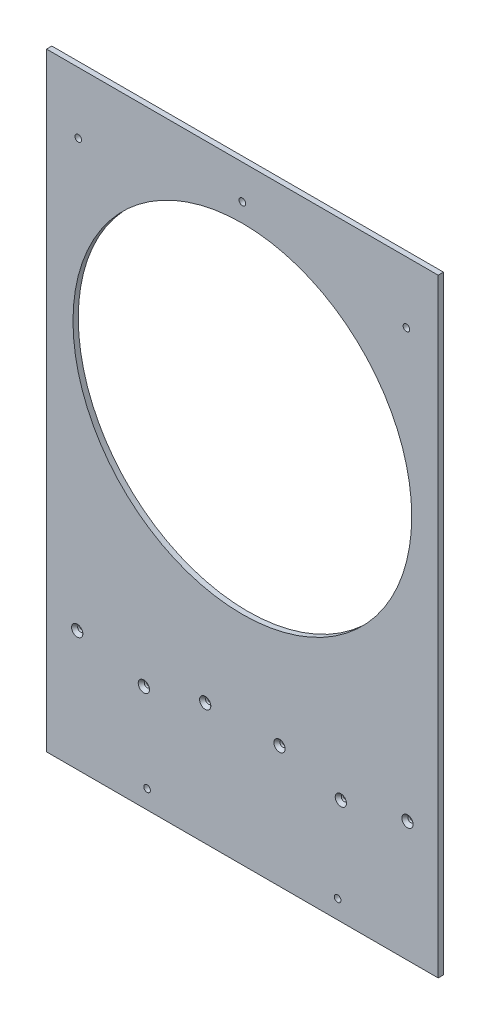
SolidWorks part; units mm, degrees
material "PC High Viscosity"
ref_plane "Front Plane" through (0, 0, 0) normal (0, 0, 1) x (1, 0, 0)
ref_plane "Top Plane" through (0, 0, 0) normal (0, 1, 0) x (1, 0, 0)
ref_plane "Right Plane" through (0, 0, 0) normal (1, 0, 0) x (0, 0, -1)
sketch "Sketch1" plane through (0, 0, 0) normal (0, 0, 1) x (1, 0, 0)
  line L0 (0, 695.96) -> (0, 1407.16) construction
  line L1 (-234.95, 0) -> (234.95, 0)
  line L2 (-234.95, 0) -> (-234.95, 2413)
  line L3 (-234.95, 2413) -> (234.95, 2413)
  line L4 (234.95, 0) -> (234.95, 2413)
  circle A0 centre (0, 695.96) radius 203.2
  circle A1 centre (0, 1407.16) radius 203.2
  circle A2 centre (0, 2118.36) radius 203.2
  dimension "D3" = 406.4
  dimension "D1" = 2413
  dimension "D2" = 469.9
  dimension "D4" = 492.76
  dimension "D6" = 711.2
  dimension "D5" = 3
extrude "Boss-Extrude1" add sketch "Sketch1" along normal blind 6.35
hole_wizard "CSK for 1/4 Flat Head Socket Cap Screw1" positions "Sketch2" profile "Sketch3" countersink size "1/4" standard "ANSI Inch"
sketch "Sketch2" plane through (0, 0, 6.35) normal (0, 0, 1) x (1, 0, 0)
  line L0 (0, 0) -> (0, 2413) construction
  line L1 (234.95, 2413) -> (-234.95, 2413) construction
  line L3 (2.839, 370.0053) -> (12.7, 406.807) construction
  line L4 (2.839, 370.0053) -> (225.089, 310.4536) construction
  line L5 (12.7, 406.807) -> (234.95, 347.2553) construction
  line L6 (225.089, 310.4536) -> (234.95, 347.2553) construction
  line L7 (234.95, 0) -> (234.95, 2413) construction
  line L8 (-234.95, 0) -> (234.95, 0) construction
  line L9 (7.7695, 388.4062) -> (230.0195, 328.8545) construction
  line L11 (118.1748, 358.8231) -> (118.1748, 1070.0231) construction
  line L12 (12.7, 406.807) -> (0, 410.21) construction
  line L14 (12.7, 406.807) -> (14.3435, 412.9407) construction
  line L15 (12.7, 406.807) -> (233.3065, 347.6957) construction
  line L16 (14.3435, 412.9407) -> (234.95, 353.8293) construction
  line L17 (233.3065, 347.6957) -> (234.95, 353.8293) construction
  circle A0 centre (198.12, 376.8459) radius 6.35 construction
  point P0 (44.5713, 378.5452)
  point P2 (118.1748, 358.8231)
  point P4 (-44.5713, 378.5452)
  point P6 (-118.1748, 358.8231)
  point P187 (44.5713, 1089.7452)
  point P188 (118.1748, 1070.0231)
  point P189 (-44.5713, 1089.7452)
  point P190 (-118.1748, 1070.0231)
  point P191 (44.5713, 1800.9452)
  point P192 (118.1748, 1781.2231)
  point P193 (-44.5713, 1800.9452)
  point P194 (-118.1748, 1781.2231)
  point P380 (198.12, 376.8459)
  point P382 (-198.12, 376.8459)
  point P386 (-198.12, 1088.0459)
  point P387 (-198.12, 1799.2459)
  point P388 (198.12, 1799.2459)
  point P389 (198.12, 1088.0459)
  point P453 (114.3, 968.375) [skipped]
  point P454 (114.3, 923.925) [skipped]
  dimension "D10" = 12.7
  dimension "D11" = 6.35
  dimension "D1" = 38.1
  dimension "D2" = 410.21
  dimension "D3" = 15
  dimension "D4" = 38.1
  dimension "D5" = 114.3
  dimension "D7" = 711.2
  dimension "D8" = 12.7
  dimension "D9" = 6.35
  dimension "D12" = 186.8565
  dimension "D13" = 198.12
  dimension "D6" = 3
sketch "Sketch3" plane through (44.5713, 378.5452, 6.35) normal (1, 0, 0) x (0, -1, 0)
  line L0 (0, 0) -> (0, 6.35)
  line L1 (0, 6.35) -> (3.3782, 6.35)
  line L2 (3.3782, 6.35) -> (3.3782, 3.8716)
  line L3 (3.3782, 3.8716) -> (6.7437, 0)
  line L5 (6.7437, 0) -> (0, 0)
  line L6 (-3.3782, 3.8716) -> (-6.7437, 0) construction
  line L11 (0, -6.35) -> (0, 107.95) construction
  dimension "Thru Hole Dia." = 6.7564
  dimension "Thru Hole Depth" = 6.35
  dimension "Near C'Sink Dia." = 13.4874
  dimension "Near C'Sink Angle" = 82
hole_wizard "5/16 (0.3125) Diameter Hole1" positions "Sketch4" profile "Sketch5" hole size "5/16" standard "ANSI Inch" end condition through all
sketch "Sketch4" plane through (0, 0, 6.35) normal (0, 0, 1) x (1, 0, 0)
  line L0 (0, 0) -> (0, 2413) construction
  line L1 (234.95, 2413) -> (-234.95, 2413) construction
  line L3 (0, 232.41) -> (-114.3, 232.41) construction
  line L5 (-114.3, 254.635) -> (-114.3, 210.185) construction
  line L7 (-234.95, 2413) -> (-234.95, 0) construction
  line L8 (-234.95, 0) -> (234.95, 0) construction
  line L9 (196.85, 1600.2) -> (196.85, 2311.4) construction
  point P0 (-114.3, 254.635)
  point P2 (-114.3, 210.185)
  point P4 (-196.85, 177.8)
  point P27 (196.85, 177.8)
  point P28 (114.3, 210.185)
  point P29 (114.3, 254.635)
  point P41 (-114.3, 965.835)
  point P42 (-114.3, 921.385)
  point P43 (-196.85, 889)
  point P44 (196.85, 889)
  point P45 (114.3, 921.385)
  point P46 (114.3, 965.835)
  point P47 (-114.3, 1677.035)
  point P48 (-114.3, 1632.585)
  point P49 (-196.85, 1600.2)
  point P50 (196.85, 1600.2)
  point P51 (114.3, 1632.585)
  point P52 (114.3, 1677.035)
  point P65 (-196.85, 2311.4)
  point P66 (196.85, 2311.4)
  point P69 (0, 2343.785)
  dimension "D1" = 114.3
  dimension "D2" = 44.45
  dimension "D3" = 38.1
  dimension "D4" = 177.8
  dimension "D5" = 232.41
  dimension "D7" = 711.2
  dimension "D9" = 711.2
  dimension "D10" = 711.2
  dimension "D6" = 3
  dimension "D8" = 2
sketch "Sketch5" plane through (-114.3, 254.635, 6.35) normal (1, 0, 0) x (0, -1, 0)
  line L0 (0, 0) -> (0, 6.35)
  line L1 (0, 6.35) -> (3.9687, 6.35)
  line L2 (3.9687, 6.35) -> (3.9687, 0)
  line L5 (3.9687, 0) -> (0, 0)
  line L11 (0, -6.35) -> (0, 107.95) construction
  dimension "Thru Hole Dia." = 7.9375
  dimension "Thru Hole Depth" = 6.35
sketch "Sketch6" plane through (0, 0, 6.35) normal (0, 0, 1) x (1, 0, 0)
  line L0 (-234.95, 2413) -> (-234.95, 0) construction
  line L1 (-234.95, 1654.81) -> (234.95, 1654.81)
  line L2 (-234.95, 1654.81) -> (-234.95, 0)
  line L3 (-234.95, 0) -> (234.95, 0)
  line L4 (234.95, 1654.81) -> (234.95, 0)
  line L5 (-114.3, 1677.035) -> (-114.3, 1632.585) construction
  point P11 (-114.3, 1654.81)
extrude "Cut-Extrude1" cut sketch "Sketch6" against normal through all
sketch "Sketch7" plane through (0, 0, 6.35) normal (0, 0, 1) x (1, 0, 0)
  line L0 (234.95, 1654.81) -> (234.95, 2413) construction
  line L1 (-234.95, 2413) -> (234.95, 2413)
  line L2 (-234.95, 2413) -> (-234.95, 2385.06)
  line L3 (-234.95, 2385.06) -> (234.95, 2385.06)
  line L4 (234.95, 2413) -> (234.95, 2385.06)
  dimension "D1" = 27.94
extrude "Cut-Extrude2" cut sketch "Sketch7" against normal through all contours L2 L1 L4 L3
